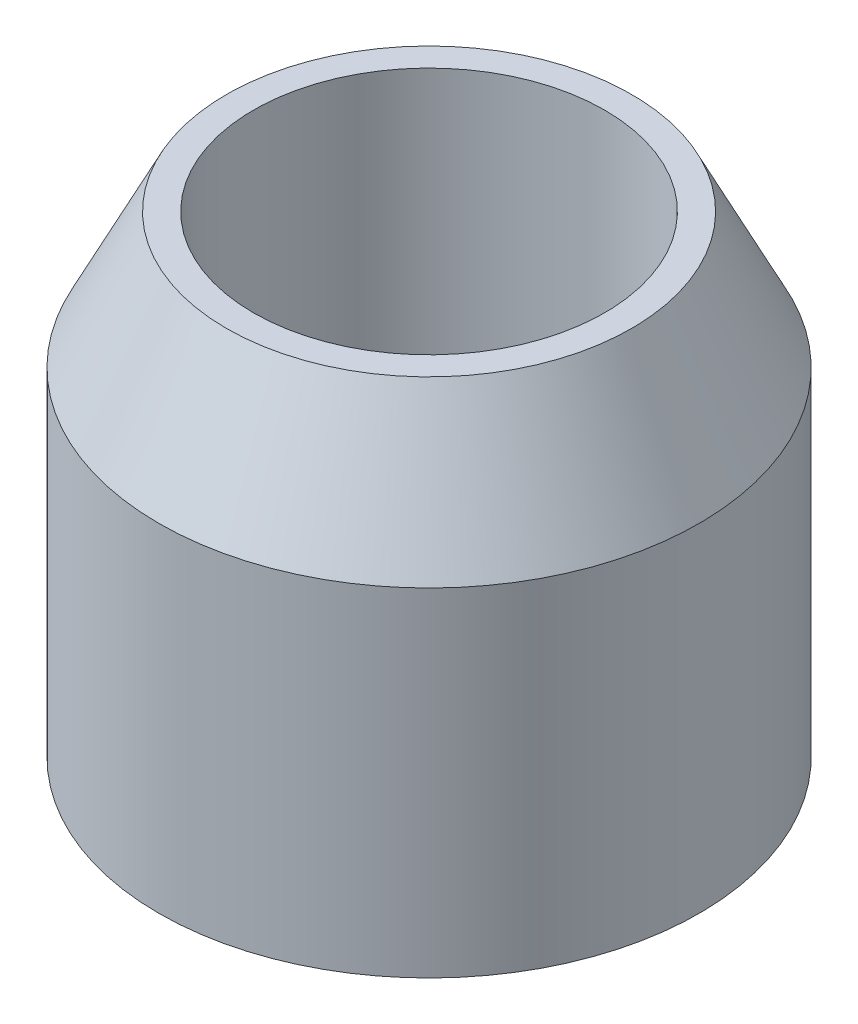
SolidWorks part; units mm, degrees
ref_plane "Front" through (0, 0, 0) normal (0, 0, 1) x (1, 0, 0)
ref_plane "Top" through (0, 0, 0) normal (0, 1, 0) x (1, 0, 0)
ref_plane "Right" through (0, 0, 0) normal (1, 0, 0) x (0, 0, -1)
sketch "Sketch1" plane through (0, 0, 0) normal (0, 1, 0) x (1, 0, 0)
  circle A0 centre (0, 0) radius 2.6
  circle A1 centre (0, 0) radius 4
  dimension "D1" = 8
  dimension "D2" = 5.2
extrude "Extrude1" add sketch "Sketch1" along normal blind 7
chamfer "Chamfer1" distance 2 distance2 1 1 edges at (0, 7, 4)
